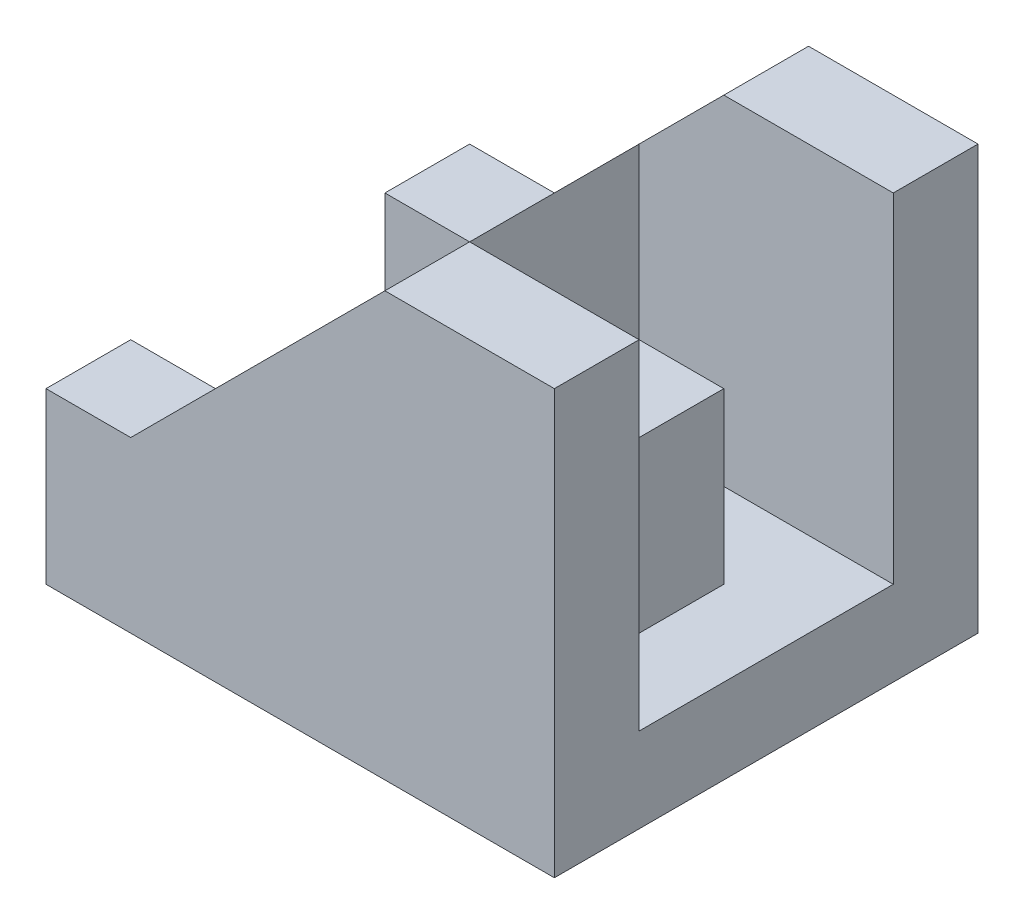
SolidWorks part; units mm, degrees
ref_plane "Front Plane" through (0, 0, 0) normal (0, 0, 1) x (1, 0, 0)
ref_plane "Top Plane" through (0, 0, 0) normal (0, 1, 0) x (1, 0, 0)
ref_plane "Right Plane" through (0, 0, 0) normal (1, 0, 0) x (0, 0, -1)
sketch "Sketch1" plane through (0, 0, 0) normal (0, 0, 1) x (1, 0, 0)
  line L0 (0, 0) -> (30, 0)
  line L1 (30, 0) -> (30, 25)
  line L2 (30, 25) -> (20, 25)
  line L3 (20, 25) -> (5, 10)
  line L4 (5, 10) -> (0, 10)
  line L5 (0, 10) -> (0, 0)
  dimension "D1" = 10
  dimension "D2" = 30
  dimension "D3" = 5
  dimension "D4" = 15
  dimension "D5" = 10
extrude "Boss-Extrude1" add sketch "Sketch1" along normal blind 25
sketch "Sketch2" plane through (0, 10, 0) normal (0, 1, 0) x (1, 0, 0)
  line L0 (0, -25) -> (0, 0) construction
  line L1 (0, -5) -> (5, -5)
  line L2 (0, -5) -> (0, -20)
  line L3 (0, -20) -> (5, -20)
  line L4 (5, -5) -> (5, -20)
  line L5 (5, -25) -> (5, 0) construction
  line L6 (5, -25) -> (0, -25) construction
  dimension "D1" = 15
  dimension "D2" = 5
extrude "Cut-Extrude1" cut sketch "Sketch2" against normal blind 25
sketch "Sketch3" plane through (0, 25, 0) normal (0, 1, 0) x (1, 0, 0)
  line L0 (30, -25) -> (30, 0) construction
  line L1 (30, -5) -> (15, -5)
  line L2 (30, -5) -> (30, -20)
  line L3 (30, -20) -> (15, -20)
  line L4 (15, -5) -> (15, -20)
  line L5 (30, -25) -> (20, -25) construction
  line L7 (15, -10) -> (25, -10)
  line L8 (15, -10) -> (15, -15)
  line L9 (15, -15) -> (25, -15)
  line L10 (25, -10) -> (25, -15)
  line M7 (20, 0) -> (20, -25)
  line M9 (30, -25) -> (30, 0)
  dimension "D1" = 15
  dimension "D2" = 5
  dimension "D3" = 15
  dimension "D4" = 10
  dimension "D5" = 5
  dimension "D6" = 5
extrude "Cut-Extrude2" cut sketch "Sketch3" against normal blind 20 contours L7 L10 L9 L3 L1 M7 M9 | L4 L7 L1 M7 | L9 L4 L3 M7
sketch "Sketch4" plane through (25, 0, 0) normal (1, 0, 0) x (0, 0, -1)
  line L0 (-10, 5) -> (-10, 20) construction
  line L1 (-15, 25) -> (-10, 25)
  line L2 (-15, 25) -> (-15, 15)
  line L3 (-15, 15) -> (-10, 15)
  line L4 (-10, 25) -> (-10, 15)
  dimension "D1" = 10
extrude "Cut-Extrude3" cut sketch "Sketch4" against normal blind 10
